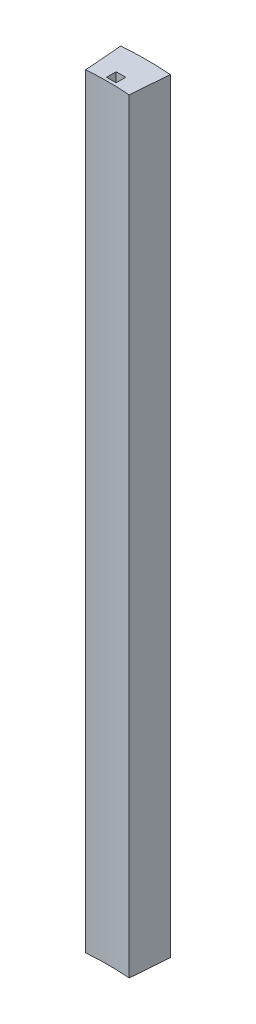
SolidWorks part; units mm, degrees
ref_plane "Front Plane" through (0, 0, 0) normal (0, 0, 1) x (1, 0, 0)
ref_plane "Top Plane" through (0, 0, 0) normal (0, 1, 0) x (1, 0, 0)
ref_plane "Right Plane" through (0, 0, 0) normal (1, 0, 0) x (0, 0, -1)
sketch "Sketch2" plane through (0, 0, 0) normal (0, 1, 0) x (1, 0, 0)
  line L0 (-4.1103, 52.226) -> (-3.6121, 45.8956)
  line L1 (4.1103, 52.226) -> (3.6121, 45.8956)
  line L2 (3.6121, 45.8956) -> (0, 0) construction
  line L3 (0, 0) -> (-3.6121, 45.8956) construction
  line L4 (-0.7938, 48.133) -> (-0.7937, 46.5455)
  line L5 (-0.7937, 46.5455) -> (0.7937, 46.5455)
  line L6 (0.7937, 46.5455) -> (0.7937, 48.133)
  line L7 (0.7937, 48.133) -> (-0.7938, 48.133)
  line L8 (0, 0) -> (0, 46.0375) construction
  line L9 (0, 46.5455) -> (0, 46.0375) construction
  arc A0 (4.1103, 52.226) -> (-4.1103, 52.226) centre (0, 0) ccw
  arc A1 (3.6121, 45.8956) -> (-3.6121, 45.8956) centre (0, 0) ccw
  point P7 (0, 46.0375)
  point P12 (0.197, 1.8417)
  point P13 (0, 0)
  point P15 (0.8752, 4.4786)
  dimension "D1" = 0.508
  dimension "D2" = 1.5875
  dimension "D3" = 46.0375
  dimension "D4" = 1.5875
  dimension "D5" = 6.35
  dimension "D6" = 9
extrude "Boss-Extrude1" add sketch "Sketch2" along normal blind 127
